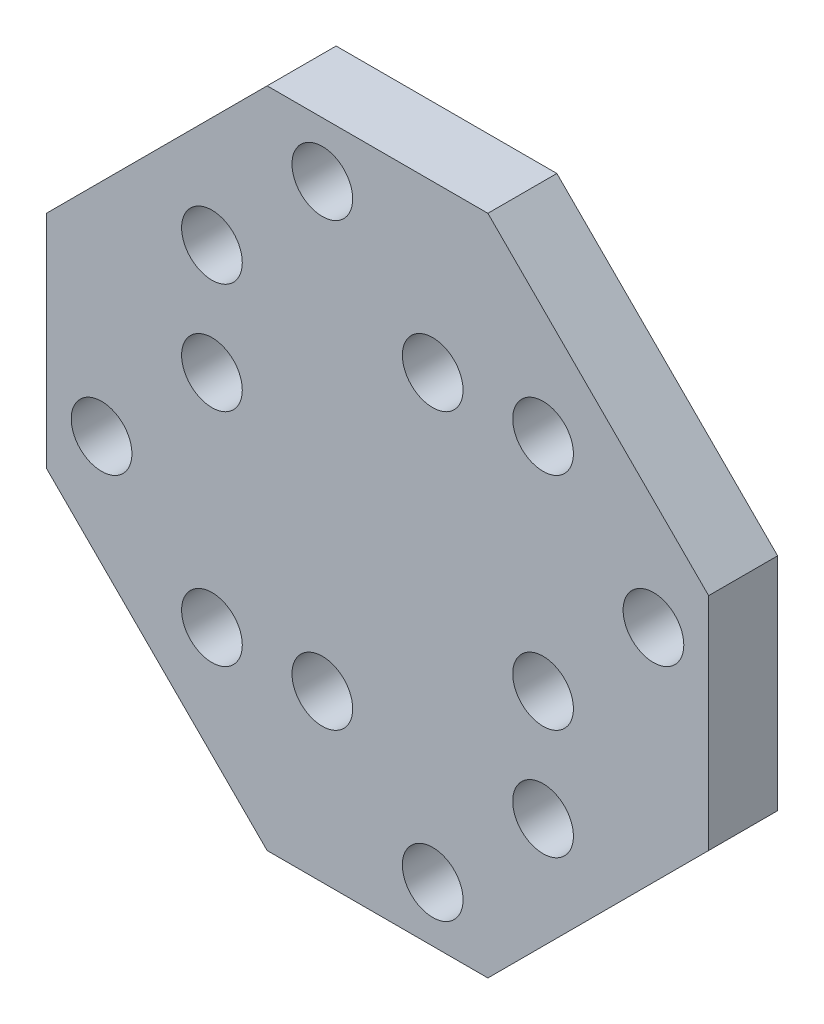
SolidWorks part; units mm, degrees
ref_plane "Ebene vorne" through (0, 0, 0) normal (0, 0, 1) x (1, 0, 0)
ref_plane "Ebene oben" through (0, 0, 0) normal (0, 1, 0) x (1, 0, 0)
ref_plane "Ebene rechts" through (0, 0, 0) normal (1, 0, 0) x (0, 0, -1)
sketch "Skizze1" plane through (0, 0, 0) normal (0, 0, 1) x (1, 0, 0)
  line L0 (-4, 12) -> (0, 8) construction
  line L5 (-4, -4) -> (4, 4) construction
  line L6 (-4, 4) -> (4, -4) construction
  line L9 (-4, 12) -> (4, 12)
  line L13 (-4, -12) -> (4, -12)
  line L18 (12, -4) -> (12, 4)
  line L22 (-12, 4) -> (-12, -4)
  line L23 (12, 4) -> (8, 0) construction
  line L24 (8, 0) -> (4, -4) construction
  line L25 (4, -12) -> (0, -8) construction
  line L26 (0, 8) -> (4, 4) construction
  line L27 (0, -8) -> (-4, -4) construction
  line L28 (-4, 4) -> (-8, 0) construction
  line L29 (-8, 0) -> (-12, -4) construction
  line L30 (0, 12) -> (0, -12) construction
  line L31 (-12, 0) -> (12, 0) construction
  line L32 (-4, 12) -> (-12, 4)
  line L33 (4, 12) -> (12, 4)
  line L34 (-12, -4) -> (-4, -12)
  line L35 (4, -12) -> (12, -4)
  line L36 (-4, 12) -> (-4, -12) construction
  line L37 (4, 12) -> (4, -12) construction
  line L38 (12, -4) -> (-12, -4) construction
  line L39 (12, 4) -> (-12, 4) construction
  line L40 (-4, 4) -> (-8, 8) construction
  line L41 (4, 4) -> (8, 8) construction
  line L42 (4, -4) -> (8, -8) construction
  line L43 (-4, -4) -> (-8, -8) construction
  circle A0 centre (-2, 10) radius 1.1
  circle A1 centre (2, 6) radius 1.1
  circle A2 centre (10, 2) radius 1.1
  circle A3 centre (6, -2) radius 1.1
  circle A4 centre (2, -10) radius 1.1
  circle A5 centre (-2, -6) radius 1.1
  circle A6 centre (-6, 2) radius 1.1
  circle A7 centre (-10, -2) radius 1.1
  circle A8 centre (-6, 6) radius 1.1
  circle A9 centre (6, 6) radius 1.1
  circle A10 centre (6, -6) radius 1.1
  circle A11 centre (-6, -6) radius 1.1
  point P0 (0, 0)
  point P1 (0, 0)
  point P31 (-11.3184, -3.3184)
  point P32 (0, 8)
  point P33 (-3.5201, -4.4799)
  point P34 (8, 0)
  point P38 (12, 0)
  point P40 (-12, 0)
  point P44 (0, -12)
  dimension "D2" = 2.2
  dimension "D1" = 8
extrude "Aufsatz-Linear austragen1" add sketch "Skizze1" along normal blind 2.5
